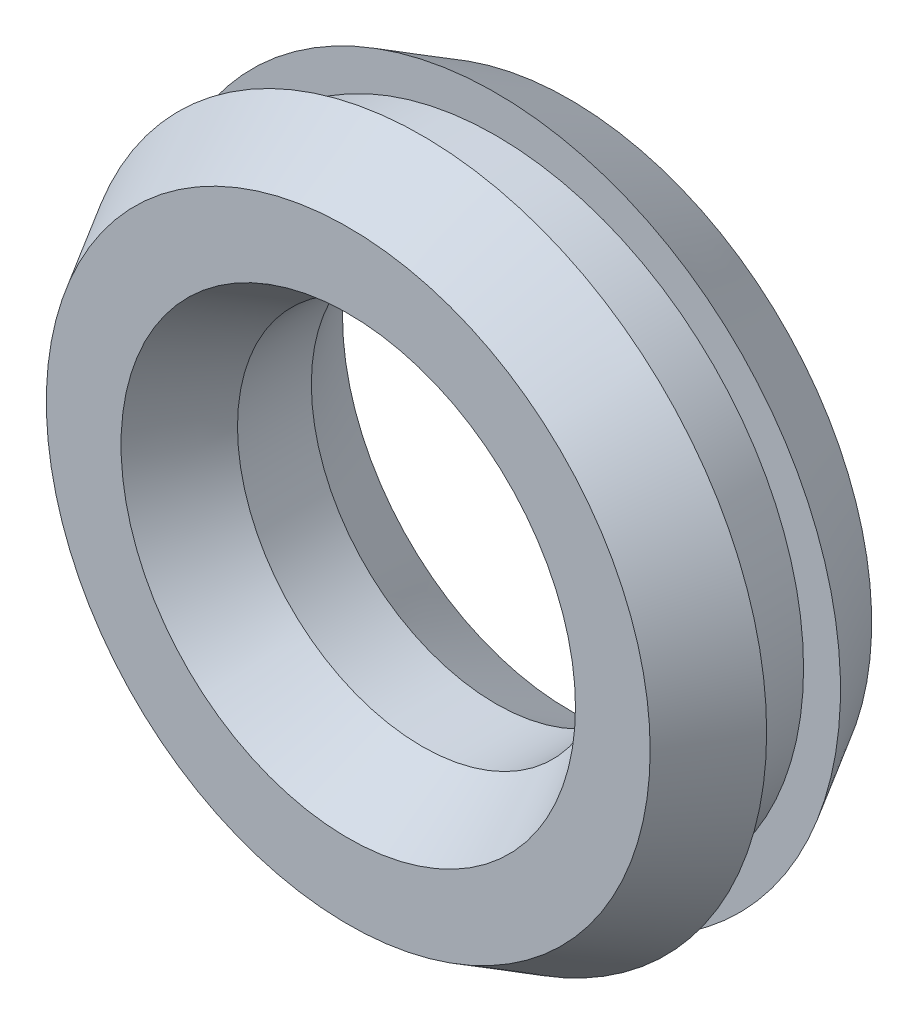
SolidWorks part; units mm, degrees
material "Wrought Stainless Steel"
ref_plane "Front Plane" through (0, 0, 0) normal (0, 0, 1) x (1, 0, 0)
ref_plane "Top Plane" through (0, 0, 0) normal (0, 1, 0) x (1, 0, 0)
ref_plane "Right Plane" through (0, 0, 0) normal (1, 0, 0) x (0, 0, -1)
sketch "Sketch1" plane through (0, 0, 0) normal (0, 0, 1) x (1, 0, 0)
  circle A0 centre (0, 0) radius 12.5
  circle A1 centre (0, 0) radius 7.5
  dimension "D1" = 25
  dimension "D2" = 15
extrude "Boss-Extrude1" add sketch "Sketch1" along normal blind 3
sketch "Sketch2" plane through (0, 0, 3) normal (0, 0, 1) x (1, 0, 0)
  circle A0 centre (0, 0) radius 14
  circle A1 centre (0, 0) radius 7.5
  dimension "D1" = 28
  dimension "D2" = 15
extrude "Boss-Extrude2" add sketch "Sketch2" along normal blind 3 draft 30
sketch "Sketch3" plane through (0, 0, 0) normal (0, 0, -1) x (-1, 0, 0)
  circle A0 centre (0, 0) radius 14
  circle A1 centre (0, 0) radius 7.5
  dimension "D1" = 28
  dimension "D2" = 15
extrude "Boss-Extrude3" add sketch "Sketch3" along normal blind 3 draft 30
